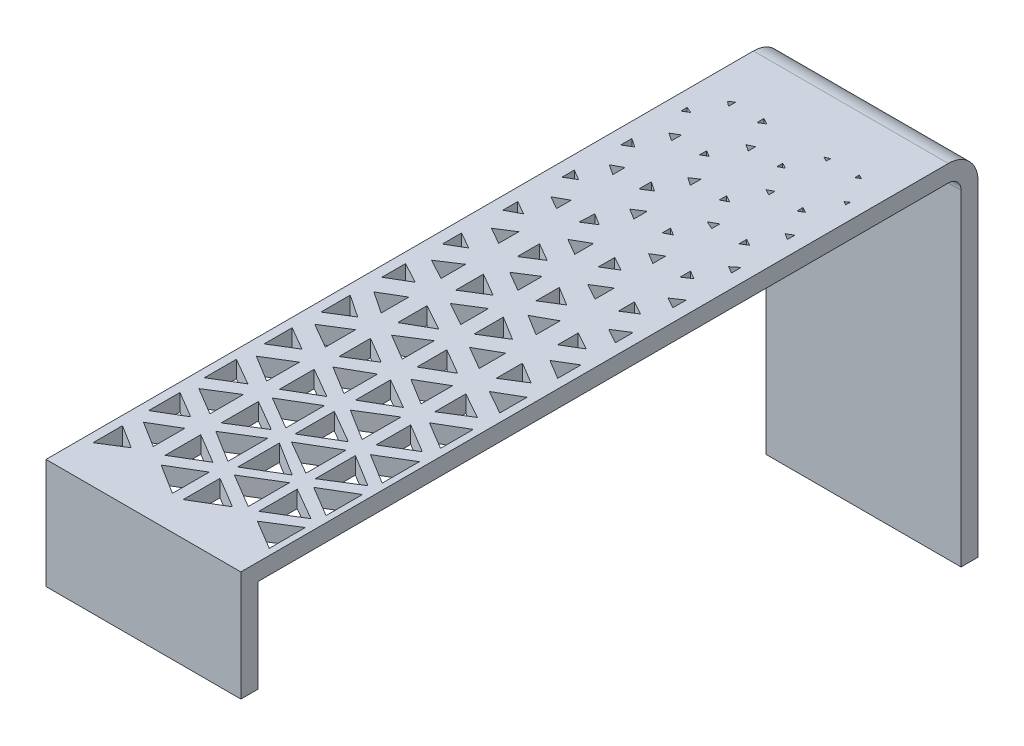
SolidWorks part; units mm, degrees
ref_plane "Front Plane" through (0, 0, 0) normal (0, 0, 1) x (1, 0, 0)
ref_plane "Top Plane" through (0, 0, 0) normal (0, 1, 0) x (1, 0, 0)
ref_plane "Right Plane" through (0, 0, 0) normal (1, 0, 0) x (0, 0, -1)
sketch "Sketch1" plane through (0, 0, 0) normal (0, 1, 0) x (1, 0, 0)
  line L1 (3.3071, 31.8366) -> (26.3071, 31.8366)
  line L2 (3.3071, 31.8366) -> (3.3071, -55.1634)
  line L3 (3.3071, -55.1634) -> (26.3071, -55.1634)
  line L4 (26.3071, 31.8366) -> (26.3071, -55.1634)
  dimension "D1" = 87
  dimension "D2" = 23
extrude "Boss-Extrude1" add sketch "Sketch1" along normal blind 42
fillet "Fillet1" radius 3.5 1 edges at (14.8071, 42, -31.8366)
sketch "Sketch2" plane through (26.3071, 0, 0) normal (1, 0, 0) x (0, 0, -1)
  line L8 (29.8366, 2) -> (29.8366, 38.5)
  line L9 (28.3366, 40) -> (-53.1634, 40)
  line L10 (-53.1634, 40) -> (-53.1634, 2)
  line L11 (-53.1634, 2) -> (29.8366, 2)
  line L12 (29.8366, 2) -> (29.8366, 38.5)
  line L13 (28.3366, 40) -> (-53.1634, 40)
  line L14 (-53.1634, 40) -> (-53.1634, 2)
  line L15 (-53.1634, 2) -> (29.8366, 2)
  arc A2 (29.8366, 38.5) -> (28.3366, 40) centre (28.3366, 38.5) ccw
  arc A3 (29.8366, 38.5) -> (28.3366, 40) centre (28.3366, 38.5) ccw
  dimension "D1" = 2
extrude "Cut-Extrude1" cut sketch "Sketch2" against normal through all
sketch "Sketch3" plane through (26.3071, 0, 0) normal (1, 0, 0) x (0, 0, -1)
  line L2 (-53.1634, 40) -> (-55.1634, 40)
  line L3 (-53.1634, 40) -> (-53.1634, 0)
  line L4 (-53.1634, 0) -> (-55.1634, 0)
  line L5 (-55.1634, 40) -> (-55.1634, 0)
extrude "Cut-Extrude3" cut sketch "Sketch3" against normal through all
sketch "Sketch4" plane through (26.3071, 0, 0) normal (1, 0, 0) x (0, 0, -1)
  line L0 (-53.1634, 0) -> (31.8366, 0) construction
  line L1 (-53.1634, 2) -> (29.8366, 2)
  line L2 (-53.1634, 2) -> (-53.1634, 0)
  line L3 (-53.1634, 0) -> (29.8366, 0)
  line L4 (29.8366, 2) -> (29.8366, 0)
extrude "Cut-Extrude5" cut sketch "Sketch4" against normal through all
sketch "Sketch6" plane through (0, 40, 0) normal (0, -1, 0) x (1, 0, 0)
  line L0 (26.3071, -28.3366) -> (26.3071, 55.1634) construction
  line L1 (3.3071, 55.1634) -> (26.3071, 55.1634)
  line L2 (3.3071, 55.1634) -> (3.3071, 53.1634)
  line L3 (3.3071, 53.1634) -> (26.3071, 53.1634)
  line L4 (26.3071, 55.1634) -> (26.3071, 53.1634)
  dimension "D1" = 2
extrude "Boss-Extrude2" add sketch "Sketch6" along normal blind 11
sketch "Sketch7" plane through (0, 42, 0) normal (0, 1, 0) x (1, 0, 0)
  line L0 (3.3071, 28.3366) -> (3.3071, -55.1634) construction
  line L1 (26.3071, -55.1634) -> (3.3071, -55.1634) construction
  line L2 (26.3071, -55.1634) -> (26.3071, -53.1634) construction
  line L3 (26.3071, -53.1634) -> (3.3071, -53.1634) construction
  line L4 (3.3071, -55.1634) -> (3.3071, -53.1634) construction
  line L5 (26.3071, -53.1634) -> (3.3071, 28.3366) construction
  line L6 (26.3071, 28.3366) -> (3.3071, -53.1634) construction
  line L7 (109.5487, 362.5536) -> (642.882, 362.5536) construction
  line L8 (4.373, -47.2039) -> (4.373, -50.682)
  line L9 (4.373, -50.682) -> (7.147, -48.9429)
  line L10 (7.147, -48.9429) -> (4.373, -47.2039)
  line L11 (10.6801, -48.9429) -> (14.2409, -51.1752)
  line L12 (14.2409, -51.1752) -> (14.2409, -46.8271)
  line L13 (14.2409, -46.8271) -> (10.6801, -48.9429)
  line L14 (15.5077, -46.8271) -> (15.5077, -51.1752)
  line L15 (15.5077, -51.1752) -> (19.1514, -49.0012)
  line L16 (19.1514, -49.0012) -> (15.5077, -46.8271)
  line L17 (22.093, -49.0012) -> (25.5747, -51.0786)
  line L18 (25.5747, -51.0786) -> (25.5747, -46.8271)
  line L19 (25.5747, -46.8271) -> (22.093, -49.0012)
  line L20 (16.0176, -45.6391) -> (20.0577, -48.0497)
  line L21 (20.0577, -48.0497) -> (20.0577, -43.1839)
  line L22 (20.0577, -43.1839) -> (16.0176, -45.6391)
  line L23 (21.1731, -43.38) -> (21.1731, -47.9142)
  line L24 (21.1731, -47.9142) -> (25.0072, -45.5841)
  line L25 (25.0072, -45.5841) -> (21.1731, -43.38)
  line L26 (21.963, -42.226) -> (25.5747, -44.3809)
  line L27 (25.5747, -44.3809) -> (25.5747, -40.0766)
  line L28 (25.5747, -40.0766) -> (21.963, -42.226)
  line L29 (19.4347, -42.226) -> (15.4019, -44.6259)
  line L30 (15.4019, -44.6259) -> (15.4019, -39.7169)
  line L31 (15.4019, -39.7169) -> (19.4347, -42.226)
  line L32 (14.2409, -39.9183) -> (14.2409, -44.6259)
  line L33 (14.2409, -44.6259) -> (10.4578, -42.2721)
  line L34 (10.4578, -42.2721) -> (14.2409, -39.9183)
  line L35 (9.9167, -43.5046) -> (9.9167, -47.7158)
  line L36 (9.9167, -47.7158) -> (13.4549, -45.6102)
  line L37 (13.4549, -45.6102) -> (9.9167, -43.5046)
  line L38 (8.3222, -43.797) -> (8.3222, -47.5178)
  line L39 (8.3222, -47.5178) -> (5.2561, -45.6102)
  line L40 (5.2561, -45.6102) -> (8.3222, -43.797)
  line L41 (4.373, -44.1168) -> (7.4924, -42.2721)
  line L42 (7.4924, -42.2721) -> (4.373, -40.4158)
  line L43 (4.373, -40.4158) -> (4.373, -44.1168)
  line L44 (5.0856, -38.9052) -> (8.3222, -40.8313)
  line L45 (8.3222, -40.8313) -> (8.3222, -36.8777)
  line L46 (8.3222, -36.8777) -> (5.0856, -38.9052)
  line L47 (9.9167, -36.7059) -> (9.9167, -41.0952)
  line L48 (9.9167, -41.0952) -> (13.5551, -38.816)
  line L49 (13.5551, -38.816) -> (9.9167, -36.7059)
  line L50 (16.0176, -38.9005) -> (20.0577, -41.2437)
  line L51 (20.0577, -41.2437) -> (20.0577, -36.5118)
  line L52 (20.0577, -36.5118) -> (16.0176, -38.9005)
  line L53 (21.1731, -36.5118) -> (21.1731, -41.2437)
  line L54 (21.1731, -41.2437) -> (24.987, -38.8545)
  line L55 (24.987, -38.8545) -> (21.1731, -36.5118)
  line L56 (21.963, -35.5303) -> (25.5747, -37.7487)
  line L57 (25.5747, -37.7487) -> (25.5747, -33.3649)
  line L58 (25.5747, -33.3649) -> (21.963, -35.5303)
  line L59 (21.303, -30.1132) -> (21.303, -34.2136)
  line L60 (21.303, -34.2136) -> (24.7226, -32.1634)
  line L61 (24.7226, -32.1634) -> (21.303, -30.1132)
  line L62 (22.1953, -28.7981) -> (25.4601, -30.7555)
  line L63 (25.4601, -30.7555) -> (25.4601, -26.874)
  line L64 (25.4601, -26.874) -> (22.1953, -28.7981)
  line L65 (21.382, -23.6861) -> (21.382, -27.356)
  line L66 (21.382, -27.356) -> (24.4811, -25.4146)
  line L67 (24.4811, -25.4146) -> (21.382, -23.6861)
  line L68 (22.5218, -22.0632) -> (25.3432, -23.6367)
  line L69 (25.3432, -23.6367) -> (25.3432, -20.4237)
  line L70 (25.3432, -20.4237) -> (22.5218, -22.0632)
  line L71 (21.5872, -17.2073) -> (21.5872, -20.3024)
  line L72 (21.5872, -20.3024) -> (24.1129, -18.7202)
  line L73 (24.1129, -18.7202) -> (21.5872, -17.2073)
  line L74 (22.9315, -15.311) -> (25.2191, -16.6812)
  line L75 (25.2191, -16.6812) -> (25.2191, -13.9297)
  line L76 (25.2191, -13.9297) -> (22.9315, -15.311)
  line L77 (21.79, -10.8356) -> (21.79, -13.2609)
  line L78 (21.79, -13.2609) -> (23.8899, -11.9929)
  line L79 (23.8899, -11.9929) -> (21.79, -10.8356)
  line L80 (23.2148, -8.6612) -> (24.987, -9.6379)
  line L81 (24.987, -9.6379) -> (24.987, -7.5416)
  line L82 (24.987, -7.5416) -> (23.2148, -8.6612)
  line L83 (21.9287, -4.3357) -> (21.9287, -6.2326)
  line L84 (21.9287, -6.2326) -> (23.5236, -5.225)
  line L85 (23.5236, -5.225) -> (21.9287, -4.3357)
  line L86 (23.5236, -1.9582) -> (24.7998, -2.6699)
  line L87 (24.7998, -2.6699) -> (24.7998, -1.098)
  line L88 (24.7998, -1.098) -> (23.5236, -1.9582)
  line L89 (22.093, 2.118) -> (22.093, 0.8786)
  line L90 (22.093, 0.8786) -> (23.08, 1.5438)
  line L91 (23.08, 1.5438) -> (22.093, 2.118)
  line L92 (23.8899, 4.8191) -> (24.7085, 4.3429)
  line L93 (24.7085, 4.3429) -> (24.7085, 5.4783)
  line L94 (24.7085, 5.4783) -> (23.8899, 4.8191)
  line L96 (22.1678, 8.6682) -> (22.1678, 7.7623)
  line L97 (22.1678, 7.7623) -> (22.9533, 8.2366)
  line L98 (22.9533, 8.2366) -> (22.1678, 8.6682)
  line L99 (24.5789, 11.9425) -> (24.5789, 11.0721)
  line L100 (24.5789, 11.0721) -> (23.8552, 11.5224)
  line L101 (23.8552, 11.5224) -> (24.5789, 11.9425)
  line L102 (22.2334, 15.2531) -> (22.2334, 14.5335)
  line L103 (22.2334, 14.5335) -> (22.863, 14.8989)
  line L104 (22.863, 14.8989) -> (22.2334, 15.2531)
  line L105 (24.0411, 18.2821) -> (24.4811, 18.0346)
  line L106 (24.4811, 18.0346) -> (24.4811, 18.5786)
  line L107 (24.4811, 18.5786) -> (24.0411, 18.2821)
  line L108 (22.2334, 21.8874) -> (22.2334, 21.3674)
  line L109 (22.2334, 21.3674) -> (22.7432, 21.6641)
  line L110 (22.7432, 21.6641) -> (22.2334, 21.8874)
  line L111 (19.0035, 8.6682) -> (19.0035, 7.7168)
  line L112 (19.0035, 7.7168) -> (18.0285, 8.1438)
  line L113 (18.0285, 8.1438) -> (19.0035, 8.6682)
  line L114 (16.5193, 11.9425) -> (16.5193, 11.0721)
  line L115 (16.5193, 11.0721) -> (17.3284, 11.5073)
  line L116 (17.3284, 11.5073) -> (16.5193, 11.9425)
  line L117 (18.2403, 14.8989) -> (18.9197, 14.5335)
  line L118 (18.9197, 14.5335) -> (18.9197, 15.2531)
  line L119 (18.9197, 15.2531) -> (18.2403, 14.8989)
  line L120 (16.5193, 18.5786) -> (16.5193, 17.9007)
  line L121 (16.5193, 17.9007) -> (17.1696, 18.2397)
  line L122 (17.1696, 18.2397) -> (16.5193, 18.5786)
  line L123 (18.8616, 21.8874) -> (18.8616, 21.3674)
  line L124 (18.8616, 21.3674) -> (18.3357, 21.6415)
  line L125 (18.3357, 21.6415) -> (18.8616, 21.8874)
  line L126 (16.5193, 5.3358) -> (16.5193, 4.3429)
  line L127 (16.5193, 4.3429) -> (17.3955, 4.7996)
  line L128 (17.3955, 4.7996) -> (16.5193, 5.3358)
  line L129 (19.0961, 2.1954) -> (19.0961, 0.6645)
  line L130 (19.0961, 0.6645) -> (17.8452, 1.4299)
  line L131 (17.8452, 1.4299) -> (19.0961, 2.1954)
  line L132 (16.2286, -0.9702) -> (16.2286, -2.9015)
  line L133 (16.2286, -2.9015) -> (17.8949, -1.8818)
  line L134 (17.8949, -1.8818) -> (16.2286, -0.9702)
  line L135 (17.3955, -5.3121) -> (19.3292, -6.37)
  line L136 (19.3292, -6.37) -> (19.3292, -4.1135)
  line L137 (19.3292, -4.1135) -> (17.3955, -5.3121)
  line L138 (10.3892, -35.5303) -> (14.2409, -37.7918)
  line L139 (16.0176, -7.2935) -> (16.0176, -10.0379)
  line L140 (16.0176, -10.0379) -> (18.252, -8.6529)
  line L141 (18.252, -8.6529) -> (16.0176, -7.2935)
  line L142 (14.2409, -37.7918) -> (14.2409, -33.234)
  line L143 (14.2409, -33.234) -> (10.3892, -35.5303)
  line L144 (15.4019, -33.234) -> (15.4019, -37.8628)
  line L145 (15.4019, -37.8628) -> (19.3434, -35.5129)
  line L146 (19.3434, -35.5129) -> (15.4019, -33.234)
  line L147 (4.3061, -33.6912) -> (4.3061, -37.4702)
  line L148 (4.3061, -37.4702) -> (7.4924, -35.5303)
  line L149 (7.4924, -35.5303) -> (4.3061, -33.6912)
  line L150 (9.9167, -34.2136) -> (13.4549, -32.1634)
  line L151 (13.4549, -32.1634) -> (9.9167, -30.1213)
  line L152 (9.9167, -30.1213) -> (9.9167, -34.2136)
  line L153 (8.3222, -30.2645) -> (8.3222, -34.1329)
  line L154 (8.3222, -34.1329) -> (5.1676, -32.1987)
  line L155 (5.1676, -32.1987) -> (8.3222, -30.2645)
  line L156 (4.373, -27.1766) -> (4.373, -30.487)
  line L157 (4.373, -30.487) -> (7.147, -28.7862)
  line L158 (7.147, -28.7862) -> (4.373, -27.1766)
  line L159 (19.9303, -29.8761) -> (19.9303, -34.4756)
  line L160 (19.9303, -34.4756) -> (16.2286, -32.1634)
  line L161 (16.2286, -32.1634) -> (19.9303, -29.8761)
  line L162 (15.5077, -26.6951) -> (15.5077, -30.8433)
  line L163 (15.5077, -30.8433) -> (19.0961, -28.764)
  line L164 (19.0961, -28.764) -> (15.5077, -26.6951)
  line L165 (14.1494, -26.874) -> (14.1494, -30.8433)
  line L166 (14.1494, -30.8433) -> (10.7943, -28.7862)
  line L167 (10.7943, -28.7862) -> (14.1494, -26.874)
  line L168 (19.7711, -23.6367) -> (19.7711, -27.356)
  line L169 (19.7711, -27.356) -> (16.6553, -25.4456)
  line L170 (16.6553, -25.4456) -> (19.7711, -23.6367)
  line L171 (15.7524, -20.3024) -> (15.7524, -23.8371)
  line L172 (15.7524, -23.8371) -> (18.7969, -22.0698)
  line L173 (18.7969, -22.0698) -> (15.7524, -20.3024)
  line L174 (16.8523, -18.7202) -> (19.5777, -20.3024)
  line L175 (19.5777, -20.3024) -> (19.5777, -17.164)
  line L176 (19.5777, -17.164) -> (16.8523, -18.7202)
  line L177 (15.7524, -13.6294) -> (15.7524, -17.0984)
  line L178 (15.7524, -17.0984) -> (18.5594, -15.3639)
  line L179 (18.5594, -15.3639) -> (15.7524, -13.6294)
  line L180 (19.4826, -10.6557) -> (19.4826, -13.506)
  line L181 (19.4826, -13.506) -> (17.0338, -11.9929)
  line L182 (17.0338, -11.9929) -> (19.4826, -10.6557)
  line L183 (10.0819, -23.6367) -> (10.0819, -27.356)
  line L184 (10.0819, -27.356) -> (13.1592, -25.4545)
  line L185 (13.1592, -25.4545) -> (10.0819, -23.6367)
  line L186 (11.0075, -22.0698) -> (14.0848, -23.8875)
  line L187 (14.0848, -23.8875) -> (14.0848, -20.1157)
  line L188 (14.0848, -20.1157) -> (11.0075, -22.0698)
  line L189 (10.0819, -16.957) -> (10.0819, -20.4237)
  line L190 (10.0819, -20.4237) -> (13.1592, -18.6666)
  line L191 (13.1592, -18.6666) -> (10.0819, -16.957)
  line L193 (11.2274, -15.3639) -> (13.9992, -16.9038)
  line L194 (13.9992, -16.9038) -> (13.9992, -13.6294)
  line L195 (13.9992, -13.6294) -> (11.2274, -15.3639)
  line L196 (10.1818, -10.411) -> (10.1818, -13.693)
  line L197 (10.1818, -13.693) -> (12.8987, -11.9929)
  line L198 (12.8987, -11.9929) -> (10.1818, -10.411)
  line L199 (13.8793, -7.1845) -> (13.8793, -10.0379)
  line L200 (13.8793, -10.0379) -> (11.5403, -8.676)
  line L201 (11.5403, -8.676) -> (13.8793, -7.1845)
  line L202 (10.3892, -3.9959) -> (10.3892, -6.6193)
  line L203 (10.3892, -6.6193) -> (12.5462, -5.2439)
  line L204 (12.5462, -5.2439) -> (10.3892, -3.9959)
  line L205 (11.6206, -1.8818) -> (13.5551, -3.0011)
  line L206 (13.5551, -3.0011) -> (13.5551, -0.7697)
  line L207 (13.5551, -0.7697) -> (11.6206, -1.8818)
  line L208 (10.6001, 2.3168) -> (10.4971, 0.5368)
  line L209 (10.4971, 0.5368) -> (11.9669, 1.474)
  line L210 (11.9669, 1.474) -> (10.6001, 2.3168)
  line L211 (12.1732, 4.8683) -> (13.429, 4.094)
  line L212 (13.429, 4.094) -> (13.429, 5.6742)
  line L213 (13.429, 5.6742) -> (12.1732, 4.8683)
  line L214 (10.6546, 8.9314) -> (10.6546, 7.4541)
  line L215 (10.6546, 7.4541) -> (11.7784, 8.1752)
  line L216 (11.7784, 8.1752) -> (10.6546, 8.9314)
  line L217 (12.3881, 11.5073) -> (13.3177, 10.8817)
  line L218 (13.3177, 10.8817) -> (13.3177, 12.1411)
  line L219 (13.3177, 12.1411) -> (12.3881, 11.5073)
  line L220 (10.7456, 15.3636) -> (10.7456, 14.5335)
  line L221 (10.7456, 14.5335) -> (11.4677, 14.9486)
  line L222 (11.4677, 14.9486) -> (10.7456, 15.3636)
  line L223 (13.2223, 18.6578) -> (13.2223, 17.7973)
  line L224 (13.2223, 17.7973) -> (12.4449, 18.3205)
  line L225 (12.4449, 18.3205) -> (13.2223, 18.6578)
  line L227 (10.8277, 22.0474) -> (10.8277, 21.2104)
  line L228 (10.8277, 21.2104) -> (11.5582, 21.6583)
  line L229 (11.5582, 21.6583) -> (10.8277, 22.0474)
  line L230 (7.4924, 22.0474) -> (7.4924, 21.2104)
  line L231 (7.4924, 21.2104) -> (6.909, 21.6583)
  line L232 (6.909, 21.6583) -> (7.4924, 22.0474)
  line L233 (5.1676, 18.6578) -> (5.1676, 17.9007)
  line L234 (5.1676, 17.9007) -> (5.8993, 18.3493)
  line L235 (5.8993, 18.3493) -> (5.1676, 18.6578)
  line L236 (7.6477, 15.4977) -> (7.6477, 14.316)
  line L237 (7.6477, 14.316) -> (6.7077, 14.9486)
  line L238 (6.7077, 14.9486) -> (7.6477, 15.4977)
  line L239 (7.6477, 8.85) -> (7.6477, 7.386)
  line L240 (7.6477, 7.386) -> (6.4488, 8.1927)
  line L241 (6.4488, 8.1927) -> (7.6477, 8.85)
  line L242 (5.0856, 12.203) -> (5.0856, 10.8817)
  line L243 (5.0856, 10.8817) -> (6.1126, 11.5114)
  line L244 (6.1126, 11.5114) -> (5.0856, 12.203)
  line L245 (5.348, -25.4964) -> (8.3222, -27.2056)
  line L246 (8.3222, -27.2056) -> (8.3222, -23.6367)
  line L247 (8.3222, -23.6367) -> (5.348, -25.4964)
  line L248 (4.4692, -20.4237) -> (4.4692, -23.8875)
  line L249 (4.4692, -23.8875) -> (7.147, -22.2133)
  line L250 (7.147, -22.2133) -> (4.4692, -20.4237)
  line L251 (5.5334, -18.6904) -> (8.1272, -20.4237)
  line L252 (8.1272, -20.4237) -> (8.1272, -17.164)
  line L253 (8.1272, -17.164) -> (5.5334, -18.6904)
  line L254 (4.5092, -13.9297) -> (4.5092, -16.7253)
  line L255 (4.5092, -16.7253) -> (6.9879, -15.2666)
  line L256 (6.9879, -15.2666) -> (4.5092, -13.9297)
  line L257 (5.7019, -12.052) -> (8.1272, -13.3601)
  line L258 (8.1272, -13.3601) -> (8.1272, -10.4578)
  line L259 (8.1272, -10.4578) -> (5.7019, -12.052)
  line L260 (4.6826, -7.4926) -> (4.6826, -9.7656)
  line L261 (4.6826, -9.7656) -> (6.6443, -8.6112)
  line L263 (6.6443, -8.6112) -> (4.6826, -7.4926)
  line L264 (5.9648, -5.2439) -> (7.9367, -6.3683)
  line L265 (7.9367, -6.3683) -> (7.9367, -3.9959)
  line L266 (7.9367, -3.9959) -> (5.9648, -5.2439)
  line L267 (4.7922, -0.9702) -> (4.7922, -2.7318)
  line L268 (4.7922, -2.7318) -> (6.4004, -1.8818)
  line L269 (6.4004, -1.8818) -> (4.7922, -0.9702)
  line L270 (6.2579, 1.474) -> (7.8054, 0.5968)
  line L271 (7.8054, 0.5968) -> (7.8054, 2.3168)
  line L272 (7.8054, 2.3168) -> (6.2579, 1.474)
  line L273 (4.9092, 5.5887) -> (4.9092, 4.1363)
  line L274 (4.9092, 4.1363) -> (6.1432, 4.8625)
  line L275 (6.1432, 4.8625) -> (4.9092, 5.5887)
  dimension "D1" = 2
extrude "Cut-Extrude6" cut sketch "Sketch7" against normal blind 2
